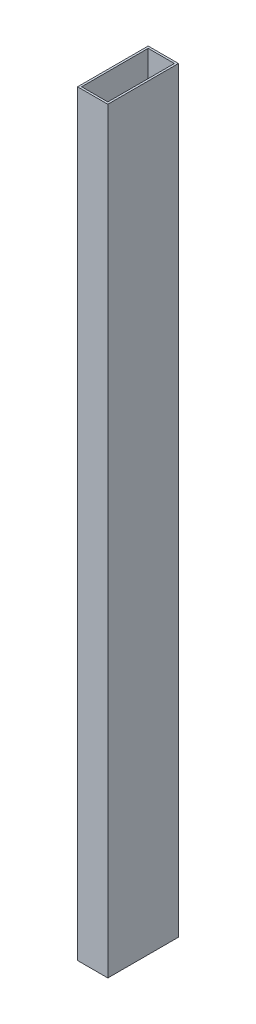
SolidWorks part; units mm, degrees
ref_plane "前视基准面" through (0, 0, 0) normal (0, 0, 1) x (1, 0, 0)
ref_plane "上视基准面" through (0, 0, 0) normal (0, 1, 0) x (1, 0, 0)
ref_plane "右视基准面" through (0, 0, 0) normal (1, 0, 0) x (0, 0, -1)
other "Configuration Table"
sketch "草图1" plane through (0, 0, 0) normal (0, 0, 1) x (1, 0, 0)
  line L1 (15, -375) -> (-15, -375)
  line L2 (15, -375) -> (15, 375)
  line L3 (15, 375) -> (-15, 375)
  line L4 (-15, -375) -> (-15, 375)
  line L5 (15, -375) -> (-15, 375) construction
  line L6 (15, 375) -> (-15, -375) construction
  point P0 (0, 0)
  dimension "D1" = 30
  dimension "D2" = 750
extrude "凸台-拉伸2" add sketch "草图1" along normal blind 70
sketch "草图2" plane through (0, -375, 0) normal (0, -1, 0) x (1, 0, 0)
  line L0 (-15, 70) -> (-15, 0) construction
  line L1 (-13, 68) -> (13, 68)
  line L2 (-13, 68) -> (-13, 2)
  line L3 (-13, 2) -> (13, 2)
  line L4 (13, 68) -> (13, 2)
  line L5 (-13, 68) -> (13, 2) construction
  line L6 (-13, 2) -> (13, 68) construction
  line L7 (-15, 70) -> (15, 70) construction
  line L8 (15, 70) -> (15, 0) construction
  line L9 (-15, 0) -> (15, 0) construction
  point P0 (0, 35)
  dimension "D1" = 2
  dimension "D2" = 2
  dimension "D3" = 2
  dimension "D4" = 2
extrude "切除-拉伸3" cut sketch "草图2" against normal through all contours L2 L1 L4 L3
